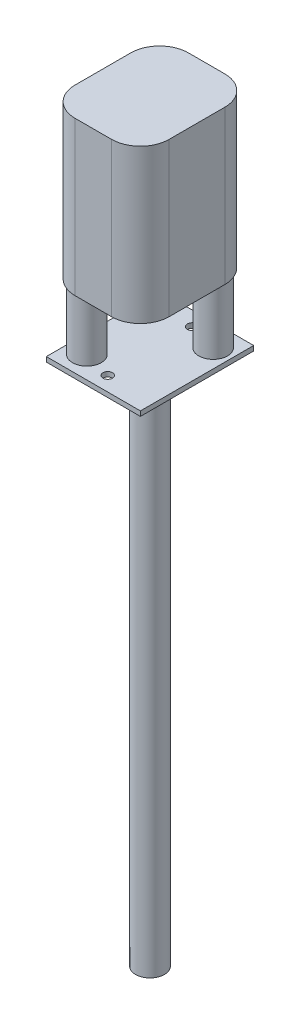
SolidWorks part; units mm, degrees
ref_plane "Front Plane" through (0, 0, 0) normal (0, 0, 1) x (1, 0, 0)
ref_plane "Top Plane" through (0, 0, 0) normal (0, 1, 0) x (1, 0, 0)
ref_plane "Right Plane" through (0, 0, 0) normal (1, 0, 0) x (0, 0, -1)
sketch "Sketch1" plane through (0, 0, 0) normal (0, 1, 0) x (1, 0, 0)
  line L1 (4.9, -5.9) -> (-4.9, -5.9)
  line L2 (4.9, -5.9) -> (4.9, 5.9)
  line L3 (4.9, 5.9) -> (-4.9, 5.9)
  line L4 (-4.9, -5.9) -> (-4.9, 5.9)
  line L5 (4.9, -5.9) -> (-4.9, 5.9) construction
  line L6 (4.9, 5.9) -> (-4.9, -5.9) construction
  point P0 (0, 0)
  dimension "D1" = 9.8
  dimension "D2" = 11.8
extrude "Boss-Extrude1" add sketch "Sketch1" along normal blind 0.5
sketch "Sketch2" plane through (0, 0, 0) normal (0, -1, 0) x (1, 0, 0)
  line L0 (0, 5.9) -> (0, -5.9) construction
  line L1 (-4.9, 5.9) -> (4.9, 5.9) construction
  line L2 (4.9, -5.9) -> (-4.9, -5.9) construction
  line L3 (-4.9, 0) -> (4.9, 0) construction
  line L4 (-4.9, -5.9) -> (-4.9, 5.9) construction
  line L5 (4.9, 5.9) -> (4.9, -5.9) construction
  circle A0 centre (0, 0) radius 1.5
  dimension "D1" = 3
extrude "Boss-Extrude2" add sketch "Sketch2" along normal blind 55 contours A0
sketch "Sketch5" plane through (0, 0, 0) normal (0, -1, 0) x (1, 0, 0)
  line L0 (0, 5.9) -> (0, -5.9) construction
  line L1 (-4.9, 5.9) -> (4.9, 5.9) construction
  line L2 (4.9, -5.9) -> (-4.9, -5.9) construction
  line L3 (-4.9, 0) -> (4.9, 0) construction
  line L4 (-4.9, -5.9) -> (-4.9, 5.9) construction
  line L5 (4.9, 5.9) -> (4.9, -5.9) construction
  circle A0 centre (0, 4.4) radius 0.5
  circle A1 centre (0, -4.4) radius 0.5
  dimension "D1" = 1
  dimension "D2" = 1.5
extrude "Cut-Extrude1" cut sketch "Sketch5" against normal blind 55
sketch "Sketch6" plane through (0, 0.5, 0) normal (0, 1, 0) x (1, 0, 0)
  line L0 (4.9, 5.9) -> (-4.9, -5.9) construction
  line L1 (-4.9, 4.0695) -> (4.9, -4.0695) construction
  line L2 (-4.9, 5.9) -> (-4.9, -5.9) construction
  line L3 (4.9, -5.9) -> (4.9, 5.9) construction
  circle A0 centre (-2.9833, -3.5921) radius 1.5
  circle A1 centre (2.9833, 3.5921) radius 1.5
  dimension "D1" = 3
  dimension "D2" = 3
extrude "Boss-Extrude3" add sketch "Sketch6" along normal blind 7
sketch "Sketch7" plane through (0, 7.5, 0) normal (0, 1, 0) x (1, 0, 0)
  line L0 (-1.9, 5.9) -> (1.9, 5.9)
  line L1 (-4.9, 2.9) -> (-4.9, -2.9071)
  line L2 (4.9, 2.9) -> (4.9, -2.9071)
  line L3 (-1.9, -5.9071) -> (1.9, -5.9071)
  arc A0 (-1.9, 5.9) -> (-4.9, 2.9) centre (-1.9, 2.9) ccw
  arc A1 (4.9, 2.9) -> (1.9, 5.9) centre (1.9, 2.9) ccw
  arc A2 (-1.9, -5.9071) -> (-4.9, -2.9071) centre (-1.9, -2.9071) cw
  arc A3 (1.9, -5.9071) -> (4.9, -2.9071) centre (1.9, -2.9071) ccw
  point P4 (-4.9, 5.9)
  point P7 (4.9, 5.9)
  dimension "D1" = 3
  dimension "D2" = 3
  dimension "D3" = 3
  dimension "D4" = 3
extrude "Boss-Extrude4" add sketch "Sketch7" along normal blind 16
